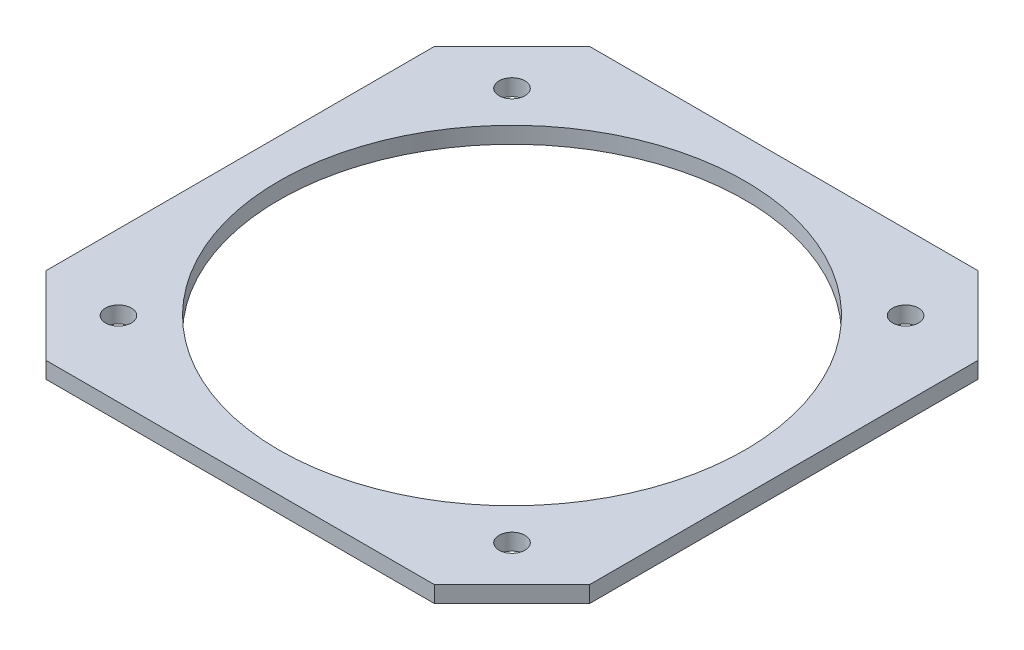
SolidWorks part; units mm, degrees
ref_plane "Front Plane" through (0, 0, 0) normal (0, 0, 1) x (1, 0, 0)
ref_plane "Top Plane" through (0, 0, 0) normal (0, 1, 0) x (1, 0, 0)
ref_plane "Right Plane" through (0, 0, 0) normal (1, 0, 0) x (0, 0, -1)
sketch "Sketch1" plane through (0, 0, 0) normal (0, 1, 0) x (1, 0, 0)
  line L1 (-105, 105) -> (105, 105)
  line L2 (-105, 105) -> (-105, -105)
  line L3 (-105, -105) -> (105, -105)
  line L4 (105, 105) -> (105, -105)
  line L5 (-105, 105) -> (105, -105) construction
  line L6 (-105, -105) -> (105, 105) construction
  circle A0 centre (0, 0) radius 90
  circle A2 centre (0, 0) radius 100 construction
  circle A3 centre (-76.014, 76.014) radius 5
  circle A5 centre (76.014, 76.014) radius 5
  circle A6 centre (76.014, -76.014) radius 5
  circle A7 centre (-76.014, -76.014) radius 5
  point P0 (0, 0)
  point P20 (0, 0)
  dimension "D3" = 180
  dimension "D4" = 10
  dimension "D5" = 200
  dimension "D6" = 107.5
  dimension "D8" = 107.5
  dimension "D1" = 210
  dimension "D2" = 210
  dimension "D7" = 4
extrude "Boss-Extrude1" add sketch "Sketch1" along normal blind 6.35
chamfer "Chamfer1" distance 30 angle 45 4 edges at (105, 3.175, 105) (-105, 3.175, 105) (-105, 3.175, -105) (105, 3.175, -105)
